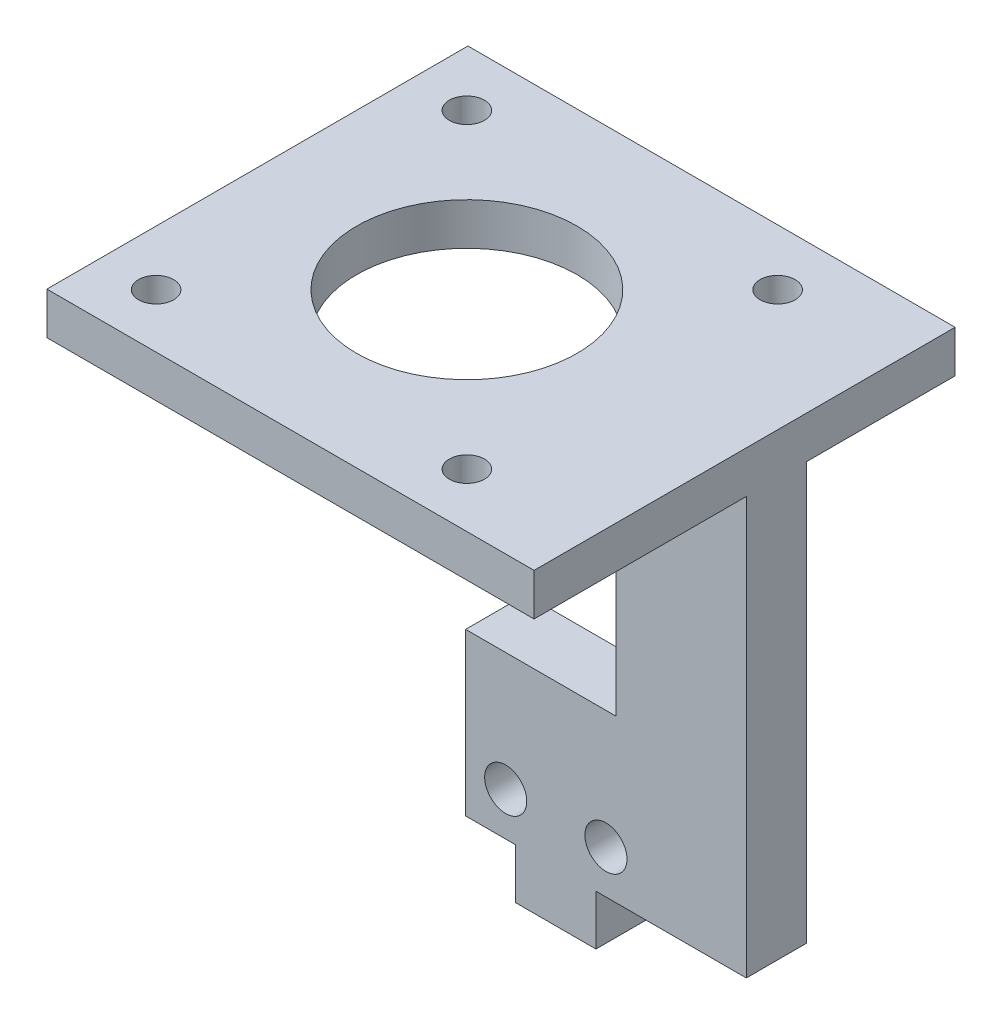
SolidWorks part; units mm, degrees
ref_plane "前视基准面" through (0, 0, 0) normal (0, 0, 1) x (1, 0, 0)
ref_plane "上视基准面" through (0, 0, 0) normal (0, 1, 0) x (1, 0, 0)
ref_plane "右视基准面" through (0, 0, 0) normal (1, 0, 0) x (0, 0, -1)
sketch "草图1" plane through (0, 0, 0) normal (0, 0, 1) x (1, 0, 0)
  line L1 (0, 0) -> (18, 0)
  line L2 (0, 0) -> (0, 50)
  line L3 (0, 50) -> (18, 50)
  line L4 (18, 0) -> (18, 50)
  dimension "D1" = 18
  dimension "D2" = 50
extrude "凸台-拉伸1" add sketch "草图1" along normal blind 6
sketch "草图3" plane through (0, 0, 6) normal (0, 0, 1) x (1, 0, 0)
  line L0 (9, 0) -> (9, 21.4804) construction
  line L1 (0, 0) -> (18, 0) construction
  circle A0 centre (4, 4.3045) radius 2.1
  circle A1 centre (14, 4.3045) radius 2.1
  dimension "D1" = 4.2
  dimension "D2" = 10
  dimension "D3" = 4.3045
extrude "切除-拉伸2" cut sketch "草图3" against normal blind 6
sketch "草图4" plane through (0, 0, 0) normal (0, -1, 0) x (1, 0, 0)
  line L0 (9, 6) -> (9, -13.3054) construction
  line L1 (0, 6) -> (18, 6) construction
  line L3 (13, 6) -> (5, 6)
  line L4 (13, 6) -> (13, -4)
  line L5 (13, -4) -> (5, -4)
  line L6 (5, 6) -> (5, -4)
  dimension "D1" = 8
  dimension "D2" = 10
extrude "凸台-拉伸2" add sketch "草图4" along normal blind 5
sketch "草图5" plane through (18, 0, 0) normal (1, 0, 0) x (0, 0, -1)
  line L0 (-6, 0) -> (-6, 50) construction
  line L1 (0, 0) -> (-6, 0)
  line L2 (0, 0) -> (0, 50)
  line L3 (0, 50) -> (-6, 50)
  line L4 (-6, 0) -> (-6, 50)
  line L5 (-6, 50) -> (0, 50) construction
  dimension "D1" = 0
extrude "凸台-拉伸3" add sketch "草图5" along normal blind 10
sketch "草图6" plane through (0, 0, 6) normal (0, 0, 1) x (1, 0, 0)
  line L0 (0, 50) -> (0, 0) construction
  line L1 (0, 16.1194) -> (15, 16.1194)
  line L2 (0, 16.1194) -> (0, 50)
  line L3 (0, 50) -> (15, 50)
  line L4 (15, 16.1194) -> (15, 50)
  line L5 (28, 50) -> (0, 50) construction
  dimension "D1" = 15
extrude "切除-拉伸3" cut sketch "草图6" against normal blind 10
sketch "草图7" plane through (0, 50, 0) normal (0, 1, 0) x (1, 0, 0)
  line L1 (28, -6) -> (9.8054, -6)
  line L2 (28, -6) -> (28, 2.4383)
  line L3 (28, 2.4383) -> (9.8054, 2.4383)
  line L4 (9.8054, -6) -> (9.8054, 2.4383)
extrude "切除-拉伸4" cut sketch "草图7" against normal blind 4.2
sketch "草图8" plane through (0, 45.8, 0) normal (0, 1, 0) x (1, 0, 0)
  line L0 (15, -6) -> (28, -6) construction
  line L1 (28, -27.17) -> (-30.5473, -27.17)
  line L2 (28, -27.17) -> (28, 14.83)
  line L3 (28, 14.83) -> (-30.5473, 14.83)
  line L4 (-30.5473, -27.17) -> (-30.5473, 14.83)
  line L5 (15, 0) -> (28, 0) construction
  dimension "D1" = 21.17
  dimension "D2" = 14.83
extrude "凸台-拉伸4" add sketch "草图8" against normal blind 4.2
sketch "草图9" plane through (-30.5473, 0, 0) normal (-1, 0, 0) x (0, 0, 1)
  line L1 (27.17, 45.8) -> (-22.0558, 45.8)
  line L2 (27.17, 45.8) -> (27.17, 39.7485)
  line L3 (27.17, 39.7485) -> (-22.0558, 39.7485)
  line L4 (-22.0558, 45.8) -> (-22.0558, 39.7485)
extrude "切除-拉伸5" cut sketch "草图9" against normal blind 9.95
sketch "草图15" plane through (0, 41.6, 0) normal (0, -1, 0) x (1, 0, 0)
  line L0 (0.4024, -12.4657) -> (0.4024, 23.6426) construction
  line L1 (0.4024, 6.2762) -> (-16.0251, 6.2762) construction
  line L2 (28, -14.83) -> (-20.5973, -14.83) construction
  line L3 (28, 0) -> (28, -14.83) construction
  circle A0 centre (15.9024, -9.2238) radius 1.75
  circle A1 centre (-15.0976, -9.2238) radius 1.75
  circle A2 centre (15.9024, 21.7762) radius 1.75
  circle A3 centre (-15.0976, 21.7762) radius 1.75
  dimension "D1" = 3.5
  dimension "D2" = 31
  dimension "D3" = 31
  dimension "D4" = 5.6062
  dimension "D5" = 12.0976
extrude "切除-拉伸6" cut sketch "草图15" against normal blind 9.95
sketch "草图16" plane through (0, 41.6, 0) normal (0, -1, 0) x (1, 0, 0)
  line L0 (-15.0976, 21.7762) -> (-15.0976, -9.2238) construction
  line L1 (-15.0976, -9.2238) -> (15.9024, -9.2238) construction
  line L2 (15.9024, -9.2238) -> (15.9024, 21.7762) construction
  line L3 (15.9024, 21.7762) -> (15.9024, 6.2762) construction
  line L4 (15.9024, 6.2762) -> (-15.0976, 6.2762) construction
  line L5 (0.4024, 6.2762) -> (0.4024, 15.207) construction
  circle A0 centre (0.4024, 6.2762) radius 11
  dimension "D1" = 22
extrude "切除-拉伸7" cut sketch "草图16" against normal blind 10
